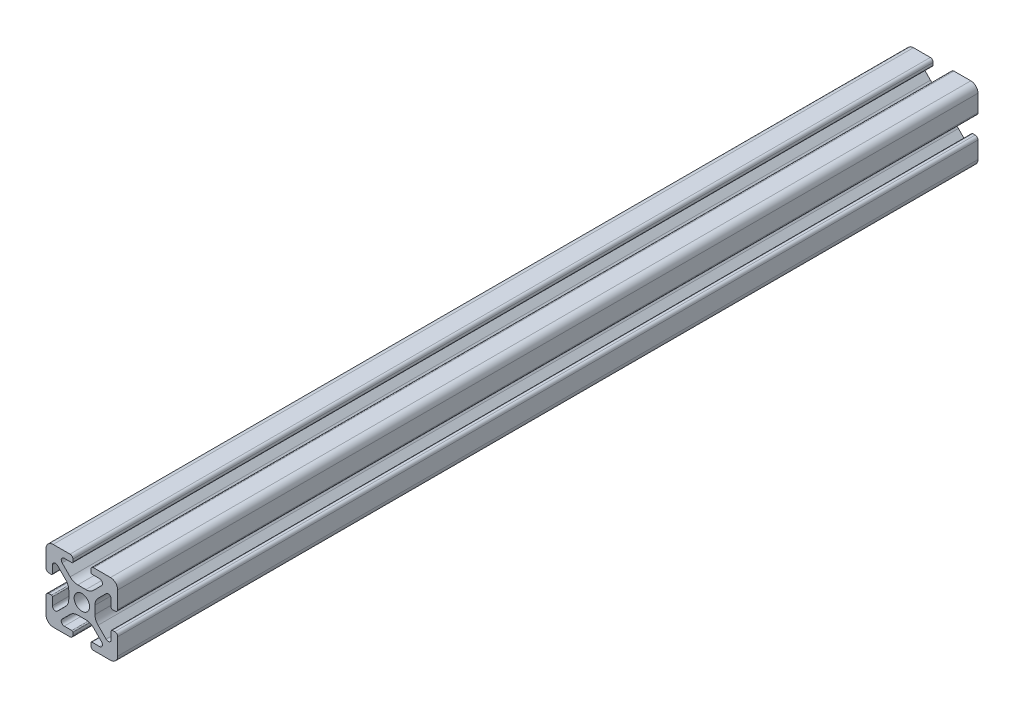
SolidWorks part; units mm, degrees
ref_plane "Front Plane" through (0, 0, 0) normal (0, 0, 1) x (1, 0, 0)
ref_plane "Top Plane" through (0, 0, 0) normal (0, 1, 0) x (1, 0, 0)
ref_plane "Right Plane" through (0, 0, 0) normal (1, 0, 0) x (0, 0, -1)
ref_plane "Plane1" through (0, 0, 0) normal (0, 0, -1) x (-1, 0, 0)
sketch "Sketch1" plane through (0, 0, 0) normal (0, 0, -1) x (-1, 0, 0)
  line L0 (-12.5, 0.8) -> (-12.5, 1.5)
  line L1 (-12.8, 1.8) -> (-14.9176, 1.8)
  line L2 (-15.5062, 3.221) -> (-13.2559, 5.4713)
  line L3 (-11.1346, 6.35) -> (-8.8654, 6.35)
  line L4 (-6.7441, 5.4713) -> (-4.4938, 3.221)
  line L5 (-5.0824, 1.8) -> (-7.2, 1.8)
  line L6 (-7.5, 1.5) -> (-7.5, 0.8)
  line L7 (-6.7, 0) -> (-2, 0)
  line L8 (0, 2) -> (0, 6.7)
  line L9 (-0.8, 7.5) -> (-1.5, 7.5)
  line L10 (-1.8, 7.2) -> (-1.8, 5.0824)
  line L11 (-3.221, 4.4938) -> (-5.4713, 6.7441)
  line L12 (-6.35, 8.8654) -> (-6.35, 11.1346)
  line L13 (-5.4713, 13.2559) -> (-3.221, 15.5062)
  line L14 (-1.8, 14.9176) -> (-1.8, 12.8)
  line L15 (-1.5, 12.5) -> (-0.8, 12.5)
  line L16 (0, 13.3) -> (0, 18)
  line L17 (-2, 20) -> (-6.7, 20)
  line L18 (-7.5, 19.2) -> (-7.5, 18.5)
  line L19 (-7.2, 18.2) -> (-5.0824, 18.2)
  line L20 (-4.4938, 16.779) -> (-6.7441, 14.5287)
  line L21 (-8.8654, 13.65) -> (-11.1346, 13.65)
  line L22 (-13.2559, 14.5287) -> (-15.5062, 16.779)
  line L23 (-14.9176, 18.2) -> (-12.8, 18.2)
  line L24 (-12.5, 18.5) -> (-12.5, 19.2)
  line L25 (-13.3, 20) -> (-18, 20)
  line L26 (-20, 18) -> (-20, 13.3)
  line L27 (-19.2, 12.5) -> (-18.5, 12.5)
  line L28 (-18.2, 12.8) -> (-18.2, 14.9176)
  line L29 (-16.779, 15.5062) -> (-14.5287, 13.2559)
  line L30 (-13.65, 11.1346) -> (-13.65, 8.8654)
  line L31 (-14.5287, 6.7441) -> (-16.779, 4.4938)
  line L32 (-18.2, 5.0824) -> (-18.2, 7.2)
  line L33 (-18.5, 7.5) -> (-19.2, 7.5)
  line L34 (-20, 6.7) -> (-20, 2)
  line L35 (-18, 0) -> (-13.3, 0)
  arc A0 (-12.5, 1.5) -> (-12.8, 1.8) centre (-12.8, 1.5) ccw
  arc A1 (-14.9176, 1.8) -> (-15.5062, 3.221) centre (-14.9176, 2.6324) cw
  arc A2 (-13.2559, 5.4713) -> (-11.1346, 6.35) centre (-11.1346, 3.35) cw
  arc A3 (-8.8654, 6.35) -> (-6.7441, 5.4713) centre (-8.8654, 3.35) cw
  arc A4 (-4.4938, 3.221) -> (-5.0824, 1.8) centre (-5.0824, 2.6324) cw
  arc A5 (-7.2, 1.8) -> (-7.5, 1.5) centre (-7.2, 1.5) ccw
  arc A6 (-7.5, 0.8) -> (-6.7, 0) centre (-6.7, 0.8) ccw
  arc A7 (-2, 0) -> (0, 2) centre (-2, 2) ccw
  arc A8 (0, 6.7) -> (-0.8, 7.5) centre (-0.8, 6.7) ccw
  arc A9 (-1.5, 7.5) -> (-1.8, 7.2) centre (-1.5, 7.2) ccw
  arc A10 (-1.8, 5.0824) -> (-3.221, 4.4938) centre (-2.6324, 5.0824) cw
  arc A11 (-5.4713, 6.7441) -> (-6.35, 8.8654) centre (-3.35, 8.8654) cw
  arc A12 (-6.35, 11.1346) -> (-5.4713, 13.2559) centre (-3.35, 11.1346) cw
  arc A13 (-3.221, 15.5062) -> (-1.8, 14.9176) centre (-2.6324, 14.9176) cw
  arc A14 (-1.8, 12.8) -> (-1.5, 12.5) centre (-1.5, 12.8) ccw
  arc A15 (-0.8, 12.5) -> (0, 13.3) centre (-0.8, 13.3) ccw
  arc A16 (0, 18) -> (-2, 20) centre (-2, 18) ccw
  arc A17 (-6.7, 20) -> (-7.5, 19.2) centre (-6.7, 19.2) ccw
  arc A18 (-7.5, 18.5) -> (-7.2, 18.2) centre (-7.2, 18.5) ccw
  arc A19 (-5.0824, 18.2) -> (-4.4938, 16.779) centre (-5.0824, 17.3676) cw
  arc A20 (-6.7441, 14.5287) -> (-8.8654, 13.65) centre (-8.8654, 16.65) cw
  arc A21 (-11.1346, 13.65) -> (-13.2559, 14.5287) centre (-11.1346, 16.65) cw
  arc A22 (-15.5062, 16.779) -> (-14.9176, 18.2) centre (-14.9176, 17.3676) cw
  arc A23 (-12.8, 18.2) -> (-12.5, 18.5) centre (-12.8, 18.5) ccw
  arc A24 (-12.5, 19.2) -> (-13.3, 20) centre (-13.3, 19.2) ccw
  arc A25 (-18, 20) -> (-20, 18) centre (-18, 18) ccw
  arc A26 (-20, 13.3) -> (-19.2, 12.5) centre (-19.2, 13.3) ccw
  arc A27 (-18.5, 12.5) -> (-18.2, 12.8) centre (-18.5, 12.8) ccw
  arc A28 (-18.2, 14.9176) -> (-16.779, 15.5062) centre (-17.3676, 14.9176) cw
  arc A29 (-14.5287, 13.2559) -> (-13.65, 11.1346) centre (-16.65, 11.1346) cw
  arc A30 (-13.65, 8.8654) -> (-14.5287, 6.7441) centre (-16.65, 8.8654) cw
  arc A31 (-16.779, 4.4938) -> (-18.2, 5.0824) centre (-17.3676, 5.0824) cw
  arc A32 (-18.2, 7.2) -> (-18.5, 7.5) centre (-18.5, 7.2) ccw
  arc A33 (-19.2, 7.5) -> (-20, 6.7) centre (-19.2, 6.7) ccw
  arc A34 (-20, 2) -> (-18, 0) centre (-18, 2) ccw
  arc A35 (-13.3, 0) -> (-12.5, 0.8) centre (-13.3, 0.8) ccw
  circle A36 centre (-10, 10) radius 2.15
extrude "Boss-Extrude1" add sketch "Sketch1" against normal blind 240
equation "\"plate_thickness\" = 6.35 'thickness of the plate "
equation "\"t_height\" = 180"
equation "\"t_width\" = 240"
equation "\"t_length\" = 240"
equation "\"D1@Boss-Extrude1\"=\"t_length\""
